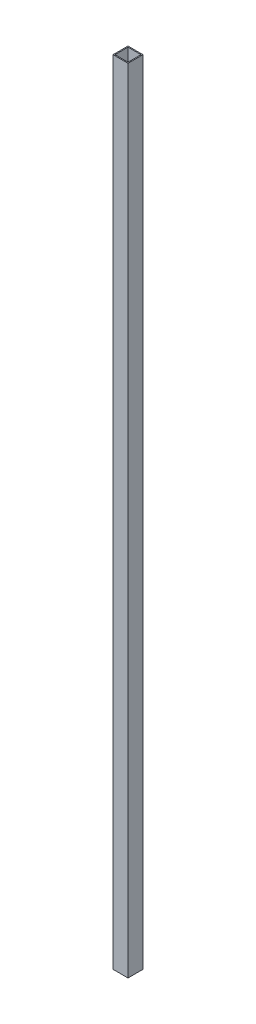
SolidWorks part; units mm, degrees
ref_plane "Front Plane" through (0, 0, 0) normal (0, 0, 1) x (1, 0, 0)
ref_plane "Top Plane" through (0, 0, 0) normal (0, 1, 0) x (1, 0, 0)
ref_plane "Right Plane" through (0, 0, 0) normal (1, 0, 0) x (0, 0, -1)
sketch "Sketch2" plane through (0, 0, 0) normal (0, 1, 0) x (1, 0, 0)
  line L1 (-15, 15) -> (15, 15)
  line L2 (-15, 15) -> (-15, -15)
  line L3 (-15, -15) -> (15, -15)
  line L4 (15, 15) -> (15, -15)
  line L5 (-15, 15) -> (15, -15) construction
  line L6 (-15, -15) -> (15, 15) construction
  line L10 (-13, 13) -> (-13, -13)
  line L11 (-13, -13) -> (13, -13)
  line L12 (13, 13) -> (13, -13)
  line L13 (-13, 13) -> (13, 13)
  point P0 (0, 0)
  dimension "D1" = 30
  dimension "D2" = 30
  dimension "D3" = 2
extrude "Boss-Extrude1" add sketch "Sketch2" along normal mid plane 1586
